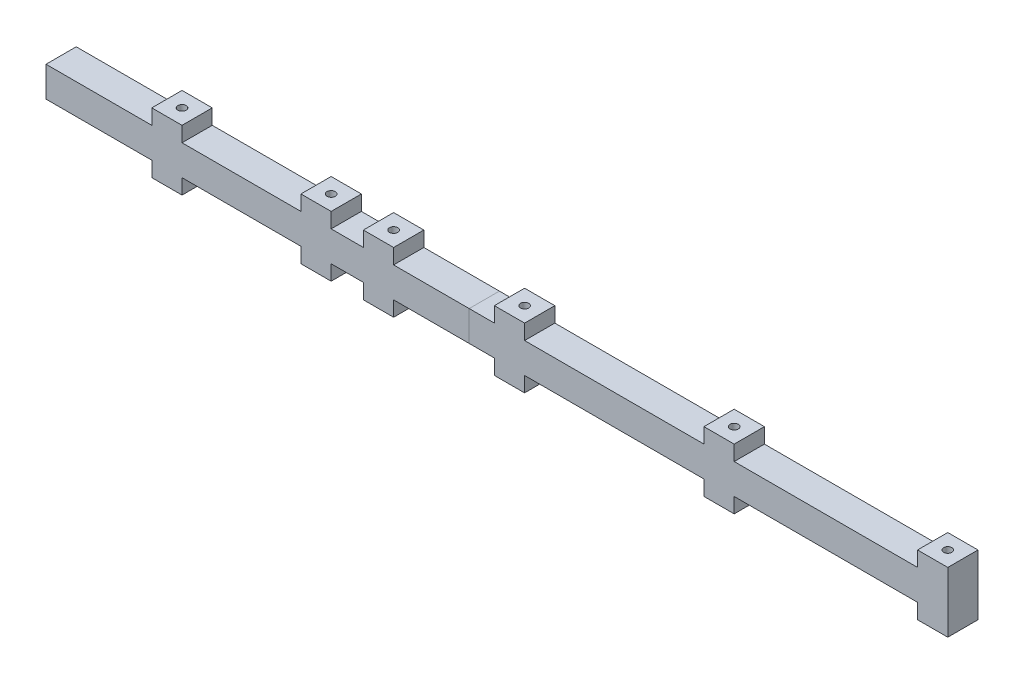
SolidWorks part; units mm, degrees
ref_plane "Front Plane" through (0, 0, 0) normal (0, 0, 1) x (1, 0, 0)
ref_plane "Top Plane" through (0, 0, 0) normal (0, 1, 0) x (1, 0, 0)
ref_plane "Right Plane" through (0, 0, 0) normal (1, 0, 0) x (0, 0, -1)
sketch "Sketch1" plane through (0, 0, 0) normal (0, 1, 0) x (1, 0, 0)
  line L1 (-200, 7.5) -> (200, 7.5)
  line L2 (-200, 7.5) -> (-200, -7.5)
  line L3 (-200, -7.5) -> (200, -7.5)
  line L4 (200, 7.5) -> (200, -7.5)
  line L5 (-200, 7.5) -> (200, -7.5) construction
  line L6 (-200, -7.5) -> (200, 7.5) construction
  point P0 (0, 0)
  dimension "D1" = 400
  dimension "D2" = 15
extrude "Boss-Extrude1" add sketch "Sketch1" along normal mid plane 15
sketch "Sketch2" plane through (0, -7.5, 0) normal (0, -1, 0) x (1, 0, 0)
  line L0 (-190, 0) -> (0, 0) construction
  line L1 (0, 0) -> (190, 0) construction
  point P0 (-190, 0)
  point P1 (-116, 0)
  point P2 (-85, 0)
  point P3 (-20, 0)
  point P4 (84, 0)
  point P5 (190, 0)
  dimension "D1" = 74
  dimension "D2" = 105
  dimension "D3" = 170
  dimension "D4" = 274
  dimension "D5" = 380
hole_wizard "Ø4.1 (4.1) Diameter Hole1" positions "Sketch2" profile "Sketch3" hole size "Ø4.1" standard "DIN" end condition through all
sketch "Sketch3" plane through (-190, -7.5, 0) normal (1, 0, 0) x (0, 0, -1)
  line L0 (0, 0) -> (0, 15)
  line L1 (0, 15) -> (2.05, 15)
  line L2 (2.05, 15) -> (2.05, 0)
  line L5 (2.05, 0) -> (0, 0)
  line L11 (0, -6.35) -> (0, 107.95) construction
  dimension "Thru Hole Dia." = 4.1
  dimension "Thru Hole Depth" = 15
sketch "Sketch4" plane through (0, 0, 0) normal (0, 1, 0) x (1, 0, 0)
  circle A0 centre (-116, 0) radius 2.05 construction
  circle A1 centre (-116, 0) radius 2.05
extrude "Boss-Extrude2" add sketch "Sketch4" along normal mid plane 5
sketch "Sketch5" plane through (0, 0, 0) normal (0, 1, 0) x (1, 0, 0)
  line L0 (-200, -7.5) -> (200, -7.5) construction
  line L1 (-197.5, 7.5) -> (-182.5, 7.5)
  line L2 (-197.5, 7.5) -> (-197.5, -7.5)
  line L3 (-197.5, -7.5) -> (-182.5, -7.5)
  line L4 (-182.5, 7.5) -> (-182.5, -7.5)
  line L5 (-197.5, 7.5) -> (-182.5, -7.5) construction
  line L6 (-197.5, -7.5) -> (-182.5, 7.5) construction
  line L7 (-123.5, 7.5) -> (-108.5, 7.5)
  line L8 (-123.5, 7.5) -> (-123.5, -7.5)
  line L9 (-123.5, -7.5) -> (-108.5, -7.5)
  line L10 (-108.5, 7.5) -> (-108.5, -7.5)
  line L11 (-123.5, 7.5) -> (-108.5, -7.5) construction
  line L12 (-123.5, -7.5) -> (-108.5, 7.5) construction
  line L13 (-92.5, 7.5) -> (-77.5, 7.5)
  line L14 (-92.5, 7.5) -> (-92.5, -7.5)
  line L15 (-92.5, -7.5) -> (-77.5, -7.5)
  line L16 (-77.5, 7.5) -> (-77.5, -7.5)
  line L17 (-92.5, 7.5) -> (-77.5, -7.5) construction
  line L18 (-92.5, -7.5) -> (-77.5, 7.5) construction
  line L19 (-27.5, 7.5) -> (-12.5, 7.5)
  line L20 (-27.5, 7.5) -> (-27.5, -7.5)
  line L21 (-27.5, -7.5) -> (-12.5, -7.5)
  line L22 (-12.5, 7.5) -> (-12.5, -7.5)
  line L23 (-27.5, 7.5) -> (-12.5, -7.5) construction
  line L24 (-27.5, -7.5) -> (-12.5, 7.5) construction
  line L25 (76.5, 7.5) -> (91.5, 7.5)
  line L26 (76.5, 7.5) -> (76.5, -7.5)
  line L27 (76.5, -7.5) -> (91.5, -7.5)
  line L28 (91.5, 7.5) -> (91.5, -7.5)
  line L29 (76.5, 7.5) -> (91.5, -7.5) construction
  line L30 (76.5, -7.5) -> (91.5, 7.5) construction
  line L31 (182.5, 7.5) -> (197.5, 7.5)
  line L32 (182.5, 7.5) -> (182.5, -7.5)
  line L33 (182.5, -7.5) -> (197.5, -7.5)
  line L34 (197.5, 7.5) -> (197.5, -7.5)
  line L35 (182.5, 7.5) -> (197.5, -7.5) construction
  line L36 (182.5, -7.5) -> (197.5, 7.5) construction
  circle A0 centre (-190, 0) radius 2.05 construction
  circle A1 centre (-190, 0) radius 2.05
  circle A2 centre (-116, 0) radius 2.05 construction
  circle A3 centre (-116, 0) radius 2.05
  circle A4 centre (-85, 0) radius 2.05 construction
  circle A5 centre (-85, 0) radius 2.05
  circle A6 centre (-20, 0) radius 2.05 construction
  circle A7 centre (-20, 0) radius 2.05
  circle A8 centre (84, 0) radius 2.05 construction
  circle A9 centre (84, 0) radius 2.05
  circle A10 centre (190, 0) radius 2.05 construction
  circle A11 centre (190, 0) radius 2.05
extrude "Boss-Extrude3" add sketch "Sketch5" along normal mid plane 30
sketch "Sketch6" plane through (-200, 0, 0) normal (-1, 0, 0) x (0, 0, 1)
  line L4 (-7.5, -7.5) -> (7.5, -7.5)
  line L5 (7.5, -7.5) -> (7.5, 7.5)
  line L6 (7.5, 7.5) -> (-7.5, 7.5)
  line L7 (-7.5, 7.5) -> (-7.5, -7.5)
  line L8 (-7.5, -7.5) -> (7.5, -7.5)
  line L9 (7.5, -7.5) -> (7.5, 7.5)
  line L10 (7.5, 7.5) -> (-7.5, 7.5)
  line L11 (-7.5, 7.5) -> (-7.5, -7.5)
  dimension "D1" = 0
extrude "Boss-Extrude5" add sketch "Sketch6" along normal blind 50
sketch "Sketch8" plane through (200, 0, 0) normal (1, 0, 0) x (0, 0, -1)
  line L4 (-7.5, -7.5) -> (7.5, -7.5)
  line L5 (7.5, -7.5) -> (7.5, 7.5)
  line L6 (7.5, 7.5) -> (-7.5, 7.5)
  line L7 (-7.5, 7.5) -> (-7.5, -7.5)
  line L8 (-7.5, -7.5) -> (7.5, -7.5)
  line L9 (7.5, -7.5) -> (7.5, 7.5)
  line L10 (7.5, 7.5) -> (-7.5, 7.5)
  line L11 (-7.5, 7.5) -> (-7.5, -7.5)
  dimension "D1" = 0
extrude "Cut-Extrude1" cut sketch "Sketch8" against normal up to surface (2.5 mm away) up to face at (197.5, 11.25, 0)
sketch "Sketch10" plane through (0, 0, 7.5) normal (0, 0, 1) x (1, 0, 0)
  line L0 (-40, 7.5) -> (-40, -7.5)
  line L1 (-12.5, 7.5) -> (76.5, 7.5) construction
  line L2 (-12.5, -7.5) -> (76.5, -7.5) construction
  line L3 (-250, -7.5) -> (-250, 7.5) construction
  dimension "D1" = 210
split "Split1" trim tools "Sketch10" bodies to split 107 resulting bodies 108 109
